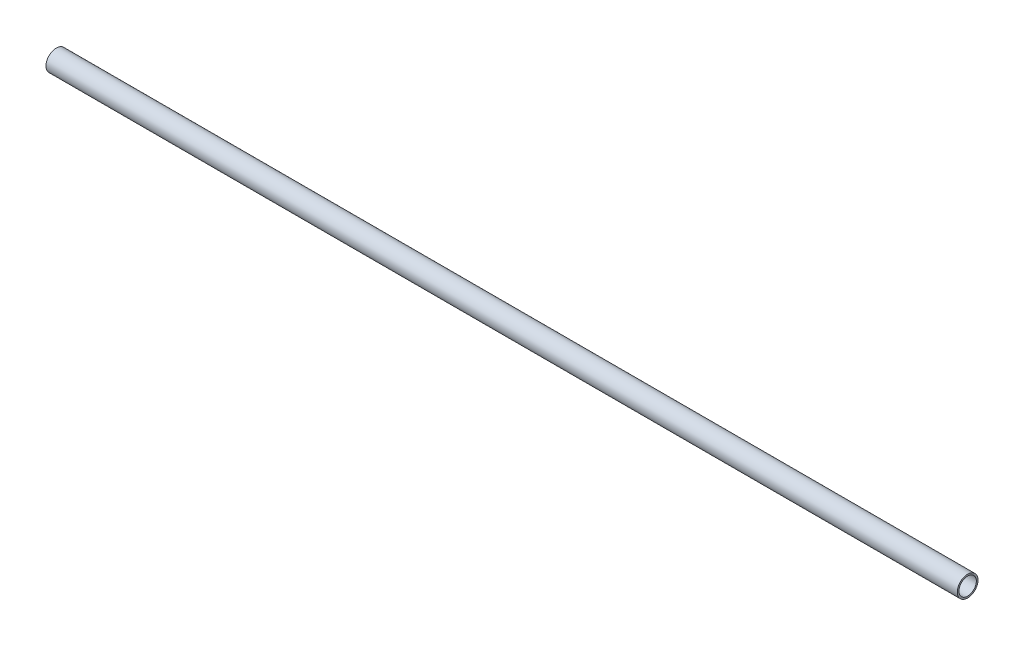
SolidWorks part; units mm, degrees
ref_plane "Front Plane" through (0, 0, 0) normal (0, 0, 1) x (1, 0, 0)
ref_plane "Top Plane" through (0, 0, 0) normal (0, 1, 0) x (1, 0, 0)
ref_plane "Right Plane" through (0, 0, 0) normal (1, 0, 0) x (0, 0, -1)
sketch "Sketch1" plane through (0, 0, 0) normal (1, 0, 0) x (0, 0, -1)
  circle A0 centre (0, 0) radius 6.35
  circle A1 centre (0, 0) radius 5.334
  dimension "D1" = 12.7
  dimension "D2" = 10.668
extrude "Boss-Extrude1" add sketch "Sketch1" against normal blind 558.8
